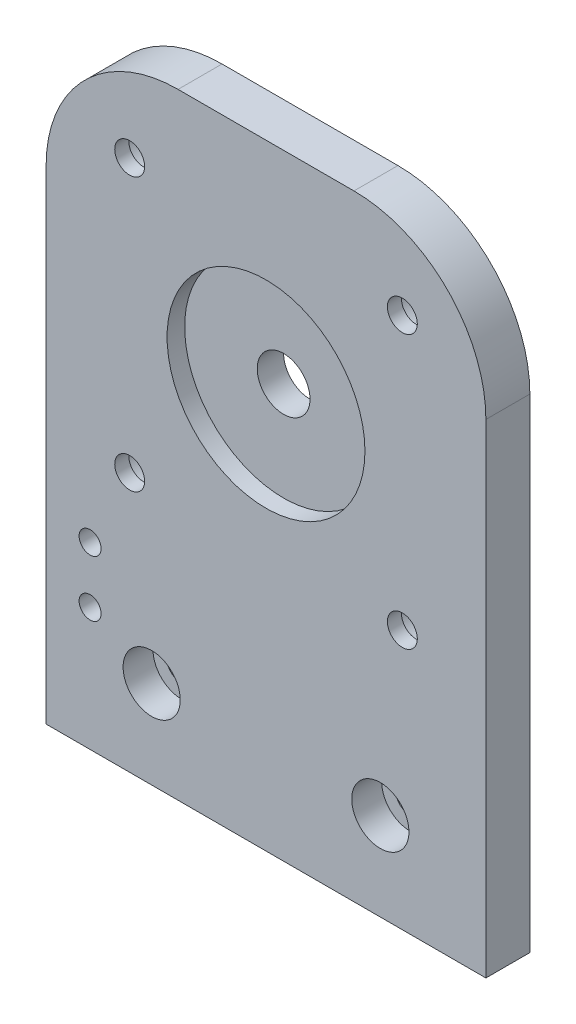
SolidWorks part; units mm, degrees
material "Allzweck-PBT"
ref_plane "Ebene vorne" through (0, 0, 0) normal (0, 0, 1) x (1, 0, 0)
ref_plane "Ebene oben" through (0, 0, 0) normal (0, 1, 0) x (1, 0, 0)
ref_plane "Ebene rechts" through (0, 0, 0) normal (1, 0, 0) x (0, 0, -1)
sketch "Skizze1" plane through (0, 0, 0) normal (0, 0, 1) x (1, 0, 0)
  line L1 (0, 0) -> (50, 0)
  line L2 (0, 0) -> (0, 55)
  line L3 (15, 70) -> (35, 70)
  line L4 (50, 0) -> (50, 55)
  arc A0 (0, 55) -> (15, 70) centre (15, 55) cw
  arc A1 (35, 70) -> (50, 55) centre (35, 55) cw
  circle A2 centre (25, 45) radius 3
  point P7 (0, 70)
  point P10 (50, 70)
  dimension "D3" = 15
  dimension "D4" = 6
  dimension "D1" = 70
  dimension "D2" = 50
  dimension "D5" = 25
  dimension "D6" = 25
extrude "Aufsatz-Linear austragen1" add sketch "Skizze1" along normal blind 5
sketch "Skizze3" plane through (0, 0, 5) normal (0, 0, 1) x (1, 0, 0)
  circle A0 centre (25, 45) radius 11.25
  dimension "D1" = 22.5
extrude "Schnitt-Linear austragen1" cut sketch "Skizze3" against normal blind 2
hole_wizard "Stirnsenkung für M3 Zylinderschraube mit Innensechskant2" positions "Skizze6" profile "Skizze7" counterbore size "M3" standard "DIN" end condition through all
sketch "Skizze6" plane through (0, 0, 0) normal (0, 0, -1) x (-1, 0, 0)
  line L3 (-50, 0) -> (-50, 55) construction
  line L5 (-35, 70) -> (-15, 70) construction
  line L6 (0, 55) -> (0, 0) construction
  point P0 (-9.5, 29.5)
  point P2 (-9.5, 60.5)
  point P4 (-40.5, 60.5)
  point P6 (-40.5, 29.5)
  dimension "D1" = 9.5
  dimension "D2" = 9.5
  dimension "D3" = 9.5
  dimension "D4" = 9.5
  dimension "D5" = 9.5
  dimension "D6" = 9.5
  dimension "D7" = 31
  dimension "D8" = 31
sketch "Skizze7" plane through (9.5, 29.5, 0) normal (1, 0, 0) x (0, 1, 0)
  line L0 (0, 0) -> (0, 5)
  line L1 (0, 5) -> (1.7, 5)
  line L3 (1.7, 5) -> (1.7, 3.4)
  line L4 (1.7, 3.4) -> (3.25, 3.4)
  line L5 (3.25, 3.4) -> (3.25, 0)
  line L7 (3.25, 0) -> (0, 0)
  line L11 (0, -6.35) -> (0, 107.95) construction
  dimension "Bohrerdurchmesser" = 3.4
  dimension "Bohrungstiefe" = 5
  dimension "Senkdurchmesser2" = 6.5
  dimension "Senktiefe2" = 3.4
hole_wizard "Stirnsenkung für M3 Zylinderschraube mit Innensechskant3" positions "Skizze8" profile "Skizze9" counterbore size "M3" standard "DIN" end condition through all
sketch "Skizze8" plane through (0, 0, 5) normal (0, 0, 1) x (1, 0, 0)
  line L0 (50, 0) -> (50, 55) construction
  line L1 (0, 55) -> (0, 0) construction
  line L2 (0, 0) -> (50, 0) construction
  point P0 (38, 10)
  point P2 (12, 10)
  dimension "D1" = 12
  dimension "D2" = 12
  dimension "D3" = 10
  dimension "D4" = 10
sketch "Skizze9" plane through (38, 10, 5) normal (1, 0, 0) x (0, -1, 0)
  line L0 (0, 0) -> (0, 5)
  line L1 (0, 5) -> (1.7, 5)
  line L3 (1.7, 5) -> (1.7, 3.4)
  line L4 (1.7, 3.4) -> (3.25, 3.4)
  line L5 (3.25, 3.4) -> (3.25, 0)
  line L7 (3.25, 0) -> (0, 0)
  line L11 (0, -6.35) -> (0, 107.95) construction
  dimension "Bohrerdurchmesser" = 3.4
  dimension "Bohrungstiefe" = 5
  dimension "Senkdurchmesser2" = 6.5
  dimension "Senktiefe2" = 3.4
hole_wizard "Ø2.5 (2.5) Durchmesser Bohrung1" positions "Skizze12" profile "Skizze14" hole size "Ø2.5" standard "ISO" end condition up to next
sketch "Skizze12" plane through (0, 0, 0) normal (0, 0, -1) x (-1, 0, 0)
  line L0 (0, 0) -> (-50, 0) construction
  line L1 (0, 55) -> (0, 0) construction
  point P0 (-5, 20.4)
  point P2 (-5, 14)
  dimension "D1" = 14
  dimension "D2" = 6.4
  dimension "D3" = 5
  dimension "D4" = 5
sketch "Skizze14" plane through (5, 20.4, 0) normal (1, 0, 0) x (0, 1, 0)
  line L0 (0, 0) -> (0, 5)
  line L1 (0, 5) -> (1.25, 5)
  line L2 (1.25, 5) -> (1.25, 0)
  line L5 (1.25, 0) -> (0, 0)
  line L11 (0, -6.35) -> (0, 107.95) construction
  dimension "Bohrerdurchmesser" = 2.5
  dimension "Bohrungstiefe" = 5
